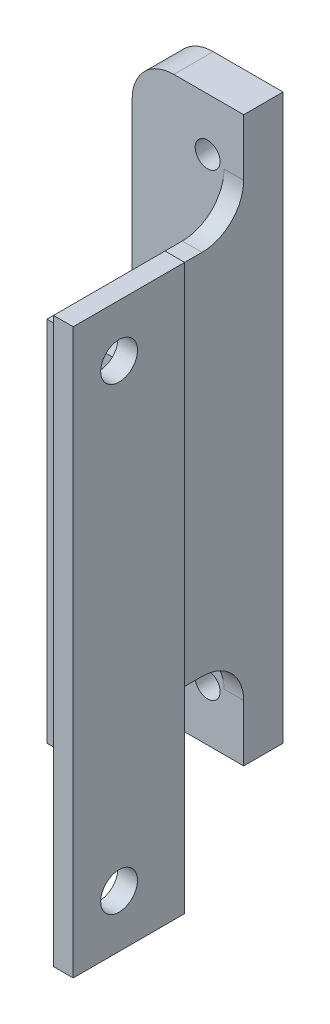
SolidWorks part; units mm, degrees
material "6061-T6 (SS)"
ref_plane "Front Plane" through (0, 0, 0) normal (0, 0, 1) x (1, 0, 0)
ref_plane "Top Plane" through (0, 0, 0) normal (0, 1, 0) x (1, 0, 0)
ref_plane "Right Plane" through (0, 0, 0) normal (1, 0, 0) x (0, 0, -1)
sketch "Sketch1" plane through (0, 0, 0) normal (0, 1, 0) x (1, 0, 0)
  line L0 (0, 0) -> (0, 17)
  line L1 (0, 17) -> (-15, 17)
  line L2 (-15, 17) -> (-15, 44)
  line L3 (-15, 44) -> (-32, 44)
  dimension "D1" = 17
  dimension "D3" = 15
  dimension "D4" = 27
  dimension "D5" = 17
extrude "Extrude-Thin1" add sketch "Sketch1" along normal mid plane 86 thin thin type one direction reverse wall 3
sketch "Sketch7" plane through (-18, 0, 0) normal (-1, 0, 0) x (0, 0, 1)
  line L0 (-14, 43) -> (-14, -43) construction
  line L1 (-41, 43) -> (-14, 43)
  line L2 (-41, 43) -> (-41, 28)
  line L3 (-41, 28) -> (-14, 28)
  line L4 (-14, 43) -> (-14, 28)
  dimension "D1" = 15
extrude "Cut-Extrude3" cut sketch "Sketch7" against normal up to surface (15 mm away) up to face at (-3, 0, -7)
mirror "Mirror3" about plane through (0, 0, 0) normal (0, 1, 0) of "Cut-Extrude3"
fillet "Fillet1" radius 6.35 2 edges at (-16.5, 28, -41) (-16.5, -28, -41)
sketch "Sketch11" plane through (0, 0, -44) normal (0, 0, -1) x (-1, 0, 0)
  line L4 (15, -43) -> (32, -43)
  line L5 (32, -43) -> (32, 43)
  line L6 (32, 43) -> (15, 43)
  line L7 (15, 43) -> (15, -43)
  line L8 (15, -43) -> (32, -43)
  line L9 (32, -43) -> (32, 43)
  line L10 (32, 43) -> (15, 43)
  line L11 (15, 43) -> (15, -43)
  dimension "D1" = 0
extrude "Boss-Extrude1" add sketch "Sketch11" along normal blind 3
hole_wizard "#10-24 Tapped Hole2" positions "Sketch5" profile "Sketch4" tap size "#10-24" standard "ANSI Inch" end condition through all
sketch "Sketch5" plane through (-13.4585, 10.0016, -47) normal (0, 0, -1) x (-1, 0, 0)
  line L2 (7.0415, 24.9984) -> (7.0415, -27.0016) construction
  line L5 (7.0415, -1.0016) -> (20.3096, -1.0016) construction
  line L6 (-13.4585, -10.0016) -> (9.445, -10.0016) construction
  line L7 (1.5415, 32.9984) -> (1.5415, -53.0016) construction
  point P0 (7.0415, -27.0016)
  point P5 (7.0415, 24.9984)
  point P32 (7.0415, 6.9984)
  point P33 (7.0415, -45.0016)
  dimension "D1" = 5.5
  dimension "D2" = 9
  dimension "D3" = 52
sketch "Sketch4" plane through (-20.5, -17, -47) normal (1, 0, 0) x (0, 1, 0)
  line L0 (0, 0) -> (0, 47)
  line L1 (0, 47) -> (1.8986, 47)
  line L2 (1.8986, 47) -> (1.8986, 0)
  line L5 (1.8986, 0) -> (0, 0)
  line L11 (0, -6.35) -> (0, 107.95) construction
  dimension "Thru Tap Drill Dia." = 3.7973
  dimension "Thru Tap Drill Depth" = 47
cosmetic thread "Hole Thread5"
cosmetic thread "Hole Thread6"
cosmetic thread "Hole Thread7"
cosmetic thread "Hole Thread8"
fillet "Fillet2" radius 6.35 2 edges at (-32, 43, -44) (-32, -43, -44)
sketch "Sketch8" plane through (-3, 0, 0) normal (-1, 0, 0) x (0, 0, 1)
  line L0 (0, 0) -> (9.6027, 0) construction
  line L1 (0, 43) -> (0, -43) construction
  line L2 (-7, -35) -> (-7, 35) construction
  point P6 (-7, 0)
  dimension "D1" = 7
  dimension "D2" = 70
hole_wizard "#10 Clearance Hole2" positions "Sketch10" profile "Sketch9" hole size "#10" standard "ANSI Inch"
sketch "Sketch10" plane through (-3, 0, 0) normal (-1, 0, 0) x (0, 0, 1)
  point P0 (-7, -35)
  point P3 (-7, 35)
sketch "Sketch9" plane through (-3, -35, -7) normal (0, 1, 0) x (0, 0, 1)
  line L0 (0, 0) -> (0, 11.2164)
  line L1 (0, 11.2164) -> (2.8067, 9.53)
  line L2 (2.8067, 9.53) -> (2.8067, 0)
  line L5 (2.8067, 0) -> (0, 0)
  line L10 (0, 11.2164) -> (-2.8067, 9.53) construction
  line L11 (0, -6.35) -> (0, 107.95) construction
  dimension "Hole Dia." = 5.6134
  dimension "Hole Depth" = 9.53
  dimension "Drill Angle" = 118
